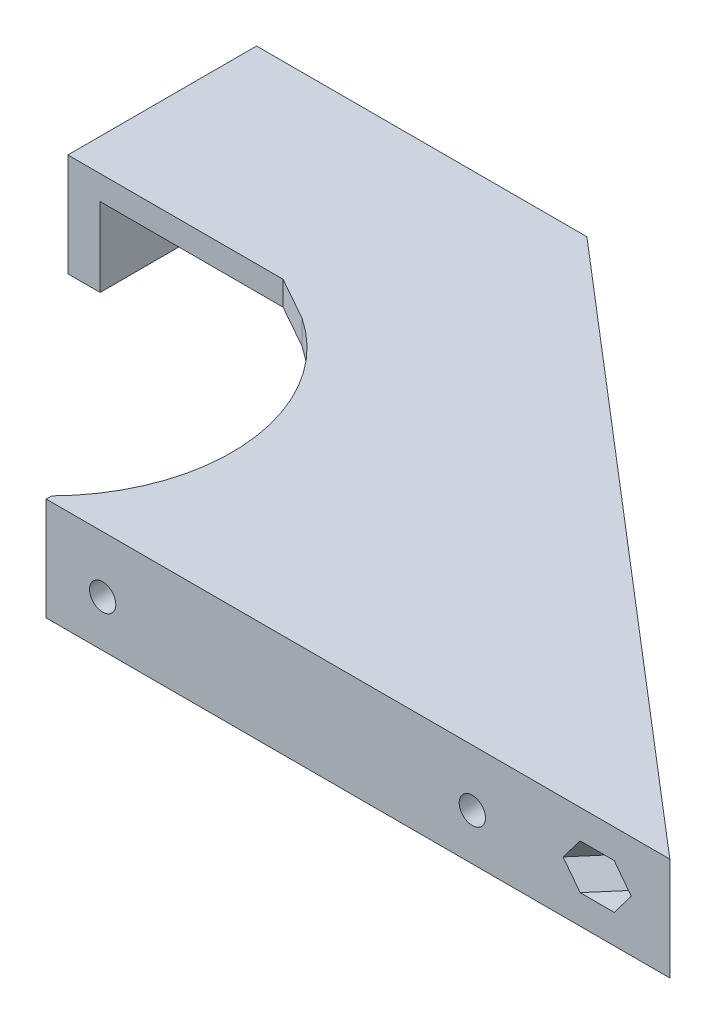
SolidWorks part; units mm, degrees
ref_plane "Alzado" through (0, 0, 0) normal (0, 0, 1) x (1, 0, 0)
ref_plane "Planta" through (0, 0, 0) normal (0, 1, 0) x (1, 0, 0)
ref_plane "Vista lateral" through (0, 0, 0) normal (1, 0, 0) x (0, 0, -1)
sketch "Croquis1" plane through (0, 0, 0) normal (0, 1, 0) x (1, 0, 0)
  line L0 (0, 0) -> (72.7832, 0)
  line L1 (72.7832, 0) -> (38.2245, 29.6204)
  line L2 (38.2245, 29.6204) -> (35.6214, 26.5833)
  line L3 (35.6214, 26.5833) -> (60.8031, 5)
  line L4 (60.8031, 5) -> (0, 5)
  line L5 (0, 5) -> (0, 0)
  dimension "D1" = 4
  dimension "D2" = 5
  dimension "D3" = 40.6
  dimension "D4" = 72.7832
extrude "Saliente-Extruir1" add sketch "Croquis1" along normal blind 12.75
sketch "Croquis2" plane through (0, 0, 0) normal (0, 0, 1) x (1, 0, 0)
  line L2 (0, 12.75) -> (72.7832, 12.75) construction
  line L3 (72.7832, 12.75) -> (72.7832, 0) construction
  circle A0 centre (52.7832, 5.75) radius 1.625
  circle A1 centre (7, 5.75) radius 1.625
  dimension "D1" = 3.25
  dimension "D2" = 20
  dimension "D3" = 7
  dimension "D4" = 45.7832
  dimension "D5" = 7
extrude "Cortar-Extruir1" cut sketch "Croquis2" against normal up to next
sketch "Croquis3" plane through (0, 12.75, 0) normal (0, 1, 0) x (1, 0, 0)
  line L0 (0, 5) -> (0, 0) construction
  line L1 (0, 0) -> (72.7832, 0) construction
  circle A0 centre (-16, 16.5) radius 22.5
  dimension "D1" = 45
  dimension "D2" = 16
  dimension "D3" = 16.5
extrude "Cortar-Extruir2" cut sketch "Croquis3" against normal through all
sketch "Croquis4" plane through (0, 12.75, 0) normal (0, 1, 0) x (1, 0, 0)
  line L0 (38.2245, 29.6204) -> (31.6563, 35.25)
  line L1 (31.6563, 35.25) -> (-3.5627, 35.25)
  line L2 (0, 0) -> (72.7832, 0) construction
  line L3 (72.7832, 0) -> (38.2245, 29.6204) construction
  line L4 (38.2245, 29.6204) -> (35.6214, 26.5833)
  line L5 (35.6214, 26.5833) -> (60.8031, 5)
  line L6 (60.8031, 5) -> (3.3391, 5)
  arc A0 (3.3391, 5) -> (-3.5627, 35.25) centre (-16, 16.5) ccw
  arc A1 (0, 0.6807) -> (3.3391, 5) centre (-16, 16.5) ccw construction
  dimension "D1" = 35.25
extrude "Saliente-Extruir2" add sketch "Croquis4" against normal blind 3
sketch "Croquis5" plane through (0, 9.75, 0) normal (0, -1, 0) x (1, 0, 0)
  line L0 (-3.5627, -35.25) -> (31.6563, -35.25)
  line L1 (31.6563, -35.25) -> (38.2245, -29.6204)
  line L2 (38.2245, -29.6204) -> (35.6214, -26.5833)
  line L3 (35.6214, -26.5833) -> (30.1767, -31.25)
  line L4 (30.1767, -31.25) -> (0.9908, -31.25)
  arc A0 (-3.5627, -35.25) -> (3.3391, -5) centre (-16, -16.5) ccw construction
  arc A1 (-3.5627, -35.25) -> (0.9908, -31.25) centre (-16, -16.5) ccw
  dimension "D1" = 4
extrude "Saliente-Extruir3" add sketch "Croquis5" along normal up to vertex (9.75 mm away)
sketch "Croquis6" plane through (30.8242, 0, -35.9632) normal (0.6508, 0, -0.7593) x (-0.7593, 0, -0.6508)
  line L0 (-55.2622, 12.75) -> (-55.2622, 0) construction
  line L1 (-1.0959, 0) -> (-1.0959, 12.75) construction
  circle A0 centre (-47.2622, 6.375) radius 1.625
  circle A1 centre (-16.0959, 6.375) radius 1.625
  dimension "D1" = 3.25
  dimension "D2" = 3.25
  dimension "D3" = 8
  dimension "D4" = 15
extrude "Cortar-Extruir3" cut sketch "Croquis6" against normal blind 10
sketch "Croquis7" plane through (28.2211, 0, -32.9261) normal (-0.6508, 0, 0.7593) x (0.7593, 0, 0.6508)
  line L1 (48.8499, 3.625) -> (50.4376, 6.375)
  line L2 (50.4376, 6.375) -> (48.8499, 9.125)
  line L3 (48.8499, 9.125) -> (45.6745, 9.125)
  line L4 (45.6745, 9.125) -> (44.0868, 6.375)
  line L5 (44.0868, 6.375) -> (45.6745, 3.625)
  line L6 (45.6745, 3.625) -> (48.8499, 3.625)
  circle A0 centre (47.2622, 6.375) radius 2.75 construction
  dimension "D1" = 5.5
extrude "Cortar-Extruir4" cut sketch "Croquis7" along normal blind 10 from offset 2 offset against normal yes
sketch "Croquis8" plane through (28.2211, 0, -32.9261) normal (-0.6508, 0, 0.7593) x (0.7593, 0, 0.6508)
  line L0 (45.6745, 3.625) -> (48.8499, 3.625) construction
  line L1 (17.6837, 3.625) -> (19.2714, 6.375)
  line L2 (19.2714, 6.375) -> (17.6837, 9.125)
  line L3 (17.6837, 9.125) -> (14.5082, 9.125)
  line L4 (14.5082, 9.125) -> (12.9205, 6.375)
  line L5 (12.9205, 6.375) -> (14.5082, 3.625)
  line L6 (14.5082, 3.625) -> (17.6837, 3.625)
  circle A0 centre (16.0959, 6.375) radius 2.75 construction
extrude "Cortar-Extruir5" cut sketch "Croquis8" along normal blind 10 from offset 2 offset against normal yes
sketch "Croquis9" plane through (0, 0, -5) normal (0, 0, -1) x (-1, 0, 0)
  line L1 (-5.4123, 3) -> (-3.8246, 5.75)
  line L2 (-3.8246, 5.75) -> (-5.4123, 8.5)
  line L3 (-5.4123, 8.5) -> (-8.5877, 8.5)
  line L4 (-8.5877, 8.5) -> (-10.1754, 5.75)
  line L5 (-10.1754, 5.75) -> (-8.5877, 3)
  line L6 (-8.5877, 3) -> (-5.4123, 3)
  line L7 (-51.1955, 3) -> (-49.6078, 5.75)
  line L8 (-49.6078, 5.75) -> (-51.1955, 8.5)
  line L9 (-51.1955, 8.5) -> (-54.3709, 8.5)
  line L10 (-54.3709, 8.5) -> (-55.9586, 5.75)
  line L11 (-55.9586, 5.75) -> (-54.3709, 3)
  line L12 (-54.3709, 3) -> (-51.1955, 3)
  circle A0 centre (-7, 5.75) radius 2.75 construction
  circle A1 centre (-52.7832, 5.75) radius 2.75 construction
  dimension "D1" = 5.5
extrude "Cortar-Extruir6" cut sketch "Croquis9" against normal blind 2
sketch "Croquis10" plane through (0, 0, -35.25) normal (0, 0, -1) x (-1, 0, 0)
  line L0 (-31.6563, 0) -> (-31.6563, 12.75) construction
  circle A0 centre (-21.6563, 6.375) radius 1.625
  dimension "D1" = 3.25
  dimension "D2" = 10
extrude "Cortar-Extruir7" cut sketch "Croquis10" against normal up to next
sketch "Croquis11" plane through (0, 0, -31.25) normal (0, 0, 1) x (1, 0, 0)
  line L1 (23.244, 3.625) -> (24.8317, 6.375)
  line L2 (24.8317, 6.375) -> (23.244, 9.125)
  line L3 (23.244, 9.125) -> (20.0686, 9.125)
  line L4 (20.0686, 9.125) -> (18.4809, 6.375)
  line L5 (18.4809, 6.375) -> (20.0686, 3.625)
  line L6 (20.0686, 3.625) -> (23.244, 3.625)
  circle A0 centre (21.6563, 6.375) radius 2.75 construction
  dimension "D1" = 5.5
extrude "Cortar-Extruir8" cut sketch "Croquis11" against normal blind 2
mirror "Simetría1" about plane through (0, 0, 0) normal (0, 1, 0) of bodies 111
sketch "Croquis12" plane through (0, 0, -35.25) normal (0, 0, -1) x (-1, 0, 0)
  line L1 (-79.3319, 0) -> (13.1768, 0)
  line L2 (-79.3319, 0) -> (-79.3319, 24.2558)
  line L3 (-79.3319, 24.2558) -> (13.1768, 24.2558)
  line L4 (13.1768, 0) -> (13.1768, 24.2558)
extrude "Cortar-Extruir9" cut sketch "Croquis12" against normal through all both and the other way through all
sketch "Croquis13" plane through (0, -12.75, 0) normal (0, -1, 0) x (1, 0, 0)
  line L1 (-35.5627, -82.3826) -> (-35.5627, -38.25)
  line L3 (-3.5627, -35.25) -> (31.6563, -35.25)
  line L5 (31.6563, -35.25) -> (0.0002, -62.3826)
  line L6 (0.0002, -62.3826) -> (-35.5627, -82.3826)
  line L7 (72.7832, 0) -> (31.6563, -35.25) construction
  line L8 (-3.5627, -35.25) -> (-8.9133, -38.25)
  line L9 (-8.9133, -38.25) -> (-35.5627, -38.25)
  dimension "D1" = 32
  dimension "D2" = 3
  dimension "D3" = 20
extrude "Saliente-Extruir4" add sketch "Croquis13" against normal up to vertex (12.75 mm away)
sketch "Croquis14" plane through (0, 0, 0) normal (0, 1, 0) x (1, 0, 0)
  line L3 (30.1767, 31.25) -> (0.9908, 31.25)
  line L4 (0.9908, 31.25) -> (-31.5627, 38.25)
  line L6 (-31.5627, 38.25) -> (-31.5627, 75.5439)
  line L7 (-2.3039, 59.0892) -> (70.1801, -3.0371)
  line L8 (-31.5627, 75.5439) -> (-2.3039, 59.0892)
  line L9 (-31.5627, 38.25) -> (-31.5627, 75.5439)
  line L10 (-2.3039, 59.0892) -> (30.1767, 31.25)
  line L11 (-31.5627, 75.5439) -> (-2.3039, 59.0892)
  dimension "D1" = 4
extrude "Cortar-Extruir10" cut sketch "Croquis14" against normal up to vertex
sketch "Croquis16" plane through (30.8242, 0, -35.9632) normal (0.6508, 0, -0.7593) x (-0.7593, 0, -0.6508)
  line L0 (40.5969, 0) -> (-55.2622, 0) construction
  line L1 (-36.0959, 0) -> (40.5969, 0)
  line L2 (-36.0959, 0) -> (-36.0959, -12.75)
  line L3 (-36.0959, -12.75) -> (40.5969, -12.75)
  line L4 (40.5969, 0) -> (40.5969, -12.75)
  circle A0 centre (-16.0959, -6.375) radius 1.625 construction
  dimension "D1" = 20
  dimension "D2" = 76.6928
extrude "Cortar-Extruir11" cut sketch "Croquis16" against normal blind 1
sketch "Croquis17" plane through (0, -12.75, 0) normal (0, -1, 0) x (1, 0, 0)
  line L1 (0.0002, -61.6233) -> (-40.6573, -61.6233)
  line L2 (0.0002, -61.6233) -> (0.0002, -84.5579)
  line L3 (0.0002, -84.5579) -> (-40.6573, -84.5579)
  line L4 (-40.6573, -61.6233) -> (-40.6573, -84.5579)
extrude "Cortar-Extruir12" cut sketch "Croquis17" against normal through all both and the other way through all
sketch "Croquis18" plane through (0, 0, 0) normal (0, 1, 0) x (1, 0, 0)
  line L0 (60.8031, 5) -> (-2.3039, 59.0892) construction
  line L1 (-35.5627, 61.6233) -> (-0.6506, 61.6233)
  line L2 (-35.5627, 61.6233) -> (-35.5627, 57.6722)
  line L3 (-35.5627, 57.6722) -> (-0.6506, 57.6722)
  line L4 (-0.6506, 61.6233) -> (-0.6506, 57.6722)
extrude "Saliente-Extruir5" add sketch "Croquis18" against normal up to surface (9.75 mm away)
sketch "Croquis20" plane through (30.1734, 0, -35.2039) normal (0.6508, 0, -0.7593) x (-0.7593, 0, -0.6508)
  line L2 (40.5969, -12.75) -> (40.5969, 0) construction
  circle A0 centre (25.5969, -6.375) radius 1.625
  circle A1 centre (-16.0959, -6.375) radius 1.625 construction
  circle A2 centre (-16.0959, -6.375) radius 1.625
  dimension "D2" = 41.6928
  dimension "D1" = 15
extrude "Cortar-Extruir14" cut sketch "Croquis20" against normal blind 10
sketch "Croquis21" plane through (28.2211, 0, -32.9261) normal (-0.6508, 0, 0.7593) x (0.7593, 0, 0.6508)
  line L0 (17.6837, -9.125) -> (14.5082, -9.125) construction
  line L1 (-24.0092, -9.125) -> (-22.4214, -6.375)
  line L2 (-22.4214, -6.375) -> (-24.0092, -3.625)
  line L3 (-24.0092, -3.625) -> (-27.1846, -3.625)
  line L4 (-27.1846, -3.625) -> (-28.7723, -6.375)
  line L5 (-28.7723, -6.375) -> (-27.1846, -9.125)
  line L6 (-27.1846, -9.125) -> (-24.0092, -9.125)
  circle A0 centre (-25.5969, -6.375) radius 2.75 construction
extrude "Cortar-Extruir15" cut sketch "Croquis21" against normal up to vertex (2 mm away) up to point (42.9493, -9.125, -22.9366)
sketch "Croquis22" plane through (0, 0, -61.6233) normal (0, 0, -1) x (-1, 0, 0)
  line L0 (35.5627, -12.75) -> (35.5627, 0) construction
  circle A0 centre (18.1127, -6.375) radius 1.625
  dimension "D1" = 3.25
  dimension "D2" = 17.45
extrude "Cortar-Extruir16" cut sketch "Croquis22" against normal blind 10
sketch "Croquis23" plane through (0, 0, -57.6722) normal (0, 0, 1) x (1, 0, 0)
  line L0 (7.5806, -9.125) -> (9.9916, -9.125) construction
  line L1 (-16.5249, -9.125) -> (-14.9372, -6.375)
  line L2 (-14.9372, -6.375) -> (-16.5249, -3.625)
  line L3 (-16.5249, -3.625) -> (-19.7004, -3.625)
  line L4 (-19.7004, -3.625) -> (-21.2881, -6.375)
  line L5 (-21.2881, -6.375) -> (-19.7004, -9.125)
  line L6 (-19.7004, -9.125) -> (-16.5249, -9.125)
  circle A0 centre (-18.1127, -6.375) radius 2.75 construction
extrude "Cortar-Extruir17" cut sketch "Croquis23" against normal blind 2
sketch "Croquis26" plane through (0, 0, 0) normal (0, 1, 0) x (1, 0, 0)
  line L0 (60.8031, 5) -> (-2.2878, 59.0754)
  line L1 (60.8031, 5) -> (60.1523, 4.2407)
  line L2 (-2.2878, 59.0754) -> (-2.9386, 58.3161)
  line L3 (60.1523, 4.2407) -> (-2.9386, 58.3161)
  line L5 (60.8031, 5) -> (-0.6506, 57.6722) construction
  dimension "D1" = 1
extrude "Saliente-Extruir6" add sketch "Croquis26" against normal up to vertex (12.75 mm away)
sketch "Croquis27" plane through (27.5703, 0, -32.1669) normal (-0.6508, 0, 0.7593) x (0.7593, 0, 0.6508)
  line L1 (-22.4214, -6.375) -> (-24.0092, -3.625)
  line L2 (-24.0092, -3.625) -> (-27.1846, -3.625)
  line L3 (-27.1846, -3.625) -> (-28.7723, -6.375)
  line L4 (-28.7723, -6.375) -> (-27.1846, -9.125)
  line L5 (-27.1846, -9.125) -> (-24.0092, -9.125)
  line L6 (-24.0092, -9.125) -> (-22.4214, -6.375)
  line L7 (19.2714, -6.375) -> (17.6837, -3.625)
  line L8 (17.6837, -3.625) -> (14.5082, -3.625)
  line L9 (14.5082, -3.625) -> (12.9205, -6.375)
  line L10 (12.9205, -6.375) -> (14.5082, -9.125)
  line L11 (14.5082, -9.125) -> (17.6837, -9.125)
  line L12 (17.6837, -9.125) -> (19.2714, -6.375)
  circle A0 centre (-25.5969, -6.375) radius 2.75 construction
  circle A1 centre (16.0959, -6.375) radius 2.75 construction
extrude "Cortar-Extruir18" cut sketch "Croquis27" against normal blind 2
sketch "Croquis28" plane through (29.5227, 0, -34.4447) normal (-0.6508, 0, 0.7593) x (0.7593, 0, 0.6508)
  line L1 (-24.0092, -3.625) -> (-27.1846, -3.625)
  line L2 (-27.1846, -3.625) -> (-28.7723, -6.375)
  line L3 (-28.7723, -6.375) -> (-27.1846, -9.125)
  line L4 (-27.1846, -9.125) -> (-24.0092, -9.125)
  line L5 (-24.0092, -9.125) -> (-22.4214, -6.375)
  line L6 (-22.4214, -6.375) -> (-24.0092, -3.625)
  line L7 (17.6837, -3.625) -> (14.5082, -3.625)
  line L8 (14.5082, -3.625) -> (12.9205, -6.375)
  line L9 (12.9205, -6.375) -> (14.5082, -9.125)
  line L10 (14.5082, -9.125) -> (17.6837, -9.125)
  line L11 (17.6837, -9.125) -> (19.2714, -6.375)
  line L12 (19.2714, -6.375) -> (17.6837, -3.625)
  circle A0 centre (-25.5969, -6.375) radius 2.75 construction
  circle A1 centre (16.0959, -6.375) radius 2.75 construction
  circle A2 centre (-25.5969, -6.375) radius 1.625
  circle A3 centre (16.0959, -6.375) radius 1.625
extrude "Saliente-Extruir7" add sketch "Croquis28" along normal blind 1
sketch "Croquis29" plane through (-35.5627, 0, 0) normal (-1, 0, 0) x (0, 0, 1)
  line L0 (-61.6233, -12.75) -> (-61.6233, 0) construction
  line L1 (-38.25, 0) -> (-61.6233, 0) construction
  circle A0 centre (-51.6233, -6.375) radius 1.9933
  dimension "D1" = 10
  dimension "D2" = 6.375
extrude "Cortar-Extruir19" cut sketch "Croquis29" against normal up to next
sketch "Croquis30" plane through (-31.5627, 0, 0) normal (1, 0, 0) x (0, 0, -1)
  line L0 (52.4097, -6.375) -> (50.8911, -6.375) construction
  line L1 (53.2381, -9.125) -> (54.8258, -6.375)
  line L2 (54.8258, -6.375) -> (53.2381, -3.625)
  line L3 (53.2381, -3.625) -> (50.0627, -3.625)
  line L4 (50.0627, -3.625) -> (48.475, -6.375)
  line L5 (48.475, -6.375) -> (50.0627, -9.125)
  line L6 (50.0627, -9.125) -> (53.2381, -9.125)
  circle A0 centre (51.6504, -6.375) radius 2.75 construction
  dimension "D1" = 5.5
extrude "Cortar-Extruir20" cut sketch "Croquis30" against normal blind 2
sketch "Croquis32" plane through (0, -12.75, 0) normal (0, -1, 0) x (1, 0, 0)
  line L0 (-0.6506, -61.6233) -> (5.3494, -61.6233)
  line L1 (5.3494, -61.6233) -> (60.1211, -14.6783)
  line L2 (60.1211, -14.6783) -> (60.7719, -15.4376)
  line L3 (60.7719, -15.4376) -> (78.7832, 0)
  line L4 (78.7832, 0) -> (72.7832, 0)
  line L5 (72.7832, 0) -> (58.2308, -12.4729)
  line L6 (58.2308, -12.4729) -> (57.58, -11.7136)
  line L7 (57.58, -11.7136) -> (-0.6506, -61.6233)
  dimension "D1" = 6
  dimension "D2" = 3.9046
  dimension "D3" = 1
extrude "Saliente-Extruir8" add sketch "Croquis32" against normal up to vertex (12.75 mm away)
sketch "Croquis33" plane through (32.7145, 0, -38.1686) normal (0.6508, 0, -0.7593) x (-0.7593, 0, -0.6508)
  line L1 (-14.5082, -3.625) -> (-17.6837, -3.625)
  line L2 (-17.6837, -3.625) -> (-19.2714, -6.375)
  line L3 (-19.2714, -6.375) -> (-17.6837, -9.125)
  line L4 (-17.6837, -9.125) -> (-14.5082, -9.125)
  line L5 (-14.5082, -9.125) -> (-12.9205, -6.375)
  line L6 (-12.9205, -6.375) -> (-14.5082, -3.625)
  line L7 (27.1846, -3.625) -> (24.0092, -3.625)
  line L8 (24.0092, -3.625) -> (22.4214, -6.375)
  line L9 (22.4214, -6.375) -> (24.0092, -9.125)
  line L10 (24.0092, -9.125) -> (27.1846, -9.125)
  line L11 (27.1846, -9.125) -> (28.7723, -6.375)
  line L12 (28.7723, -6.375) -> (27.1846, -3.625)
  circle A0 centre (-16.0959, -6.375) radius 2.75 construction
  circle A1 centre (25.5969, -6.375) radius 2.75 construction
extrude "Saliente-Extruir9" add sketch "Croquis33" along normal blind 5 from vertex at -2.9046
sketch "Croquis34" plane through (33.3652, 0, -38.9279) normal (0.6508, 0, -0.7593) x (-0.7593, 0, -0.6508)
  line L1 (-45.6745, -3.625) -> (-48.8499, -3.625)
  line L2 (-48.8499, -3.625) -> (-50.4376, -6.375)
  line L3 (-50.4376, -6.375) -> (-48.8499, -9.125)
  line L4 (-48.8499, -9.125) -> (-45.6745, -9.125)
  line L5 (-45.6745, -9.125) -> (-44.0868, -6.375)
  line L6 (-44.0868, -6.375) -> (-45.6745, -3.625)
  circle A0 centre (-47.2622, -6.375) radius 2.75 construction
extrude "Saliente-Extruir10" add sketch "Croquis34" against normal up to surface (12.1223 mm away)
sketch "Croquis35" plane through (0, 0, 0) normal (0, 1, 0) x (1, 0, 0)
  line L0 (-2.1872, 57.6722) -> (3.8128, 57.6722)
  line L1 (3.8128, 57.6722) -> (65.2664, 5)
  line L2 (65.2664, 5) -> (59.2664, 5)
  line L3 (59.2664, 5) -> (-2.1872, 57.6722)
  line L4 (5.3494, 61.6233) -> (60.1211, 14.6783) construction
  line L5 (3.3391, 5) -> (59.2664, 5) construction
  dimension "D1" = 6
extrude "Cortar-Extruir21" cut sketch "Croquis35" against normal up to surface (9.75 mm away)
sketch "Croquis36" plane through (33.3652, 0, -38.9279) normal (0.6508, 0, -0.7593) x (-0.7593, 0, -0.6508)
  line L0 (-59.8178, 0) -> (-59.8178, -12.75) construction
  line L1 (-36.0959, 0) -> (-59.8178, 0) construction
  circle A0 centre (-51.8178, -6.375) radius 1.625
  circle A1 centre (-20.6478, -6.375) radius 1.625
  circle A2 centre (21.0422, -6.375) radius 1.625
  dimension "D1" = 3.25
  dimension "D3" = 31.17
  dimension "D4" = 41.69
  dimension "D5" = 6.375
  dimension "D2" = 8
extrude "Cortar-Extruir22" cut sketch "Croquis36" against normal blind 15
sketch "Croquis38" plane through (30.1114, 0, -35.1315) normal (-0.6508, 0, 0.7593) x (0.7593, 0, 0.6508)
  line L1 (-19.44, -9.15) -> (-17.8379, -6.375)
  line L2 (-17.8379, -6.375) -> (-19.44, -3.6)
  line L3 (-19.44, -3.6) -> (-22.6443, -3.6)
  line L4 (-22.6443, -3.6) -> (-24.2465, -6.375)
  line L5 (-24.2465, -6.375) -> (-22.6443, -9.15)
  line L6 (-22.6443, -9.15) -> (-19.44, -9.15)
  line L7 (22.25, -9.15) -> (23.8521, -6.375)
  line L8 (23.8521, -6.375) -> (22.25, -3.6)
  line L9 (22.25, -3.6) -> (19.0457, -3.6)
  line L10 (19.0457, -3.6) -> (17.4435, -6.375)
  line L11 (17.4435, -6.375) -> (19.0457, -9.15)
  line L12 (19.0457, -9.15) -> (22.25, -9.15)
  circle A0 centre (-21.0422, -6.375) radius 2.775 construction
  circle A1 centre (20.6478, -6.375) radius 2.775 construction
  dimension "D1" = 5.55
extrude "Cortar-Extruir23" cut sketch "Croquis38" against normal blind 2
sketch "Croquis39" plane through (33.3652, 0, -38.9279) normal (0.6508, 0, -0.7593) x (-0.7593, 0, -0.6508)
  line L1 (-50.2157, -9.15) -> (-48.6135, -6.375)
  line L2 (-48.6135, -6.375) -> (-50.2157, -3.6)
  line L3 (-50.2157, -3.6) -> (-53.42, -3.6)
  line L4 (-53.42, -3.6) -> (-55.0221, -6.375)
  line L5 (-55.0221, -6.375) -> (-53.42, -9.15)
  line L6 (-53.42, -9.15) -> (-50.2157, -9.15)
  circle A0 centre (-51.8178, -6.375) radius 2.775 construction
  dimension "D1" = 5.55
extrude "Cortar-Extruir24" cut sketch "Croquis39" against normal through all from offset 2 offset against normal yes
mirror "Simetría2" of bodies 136 118
sketch "Croquis19" plane through (0, 0, -61.6233) normal (0, 0, -1) x (-1, 0, 0)
  line L1 (-78.7832, -12.75) -> (41.6655, -12.75)
  line L2 (-78.7832, -12.75) -> (-78.7832, 20.1367)
  line L3 (-78.7832, 20.1367) -> (41.6655, 20.1367)
  line L4 (41.6655, -12.75) -> (41.6655, 20.1367)
  line L5 (-78.7832, 0) -> (-78.7832, -25.5) construction
extrude "Cortar-Extruir13" cut sketch "Croquis19" against normal through all both and the other way through all
sketch "Croquis40" plane through (0, -25.5, 0) normal (0, -1, 0) x (1, 0, 0)
  line L0 (60.1211, -14.6783) -> (60.7719, -15.4376)
  line L1 (60.1211, -14.6783) -> (81.2695, 3.4481)
  line L2 (60.7719, -15.4376) -> (81.9203, 2.6888)
  line L3 (81.2695, 3.4481) -> (81.9203, 2.6888)
extrude "Cortar-Extruir25" cut sketch "Croquis40" against normal through all both and the other way through all
sketch "Croquis42" plane through (32.0637, 0, -37.4094) normal (-0.6508, 0, 0.7593) x (0.7593, 0, 0.6508)
  line L1 (53.42, -16.35) -> (50.2157, -16.35)
  line L2 (50.2157, -16.35) -> (48.6135, -19.125)
  line L3 (48.6135, -19.125) -> (50.2157, -21.9)
  line L4 (50.2157, -21.9) -> (53.42, -21.9)
  line L5 (53.42, -21.9) -> (55.0221, -19.125)
  line L6 (55.0221, -19.125) -> (53.42, -16.35)
  circle A0 centre (51.8178, -19.125) radius 1.625
  circle A1 centre (51.8178, -19.125) radius 2.775 construction
extrude "Saliente-Extruir11" add sketch "Croquis42" along normal blind 1
